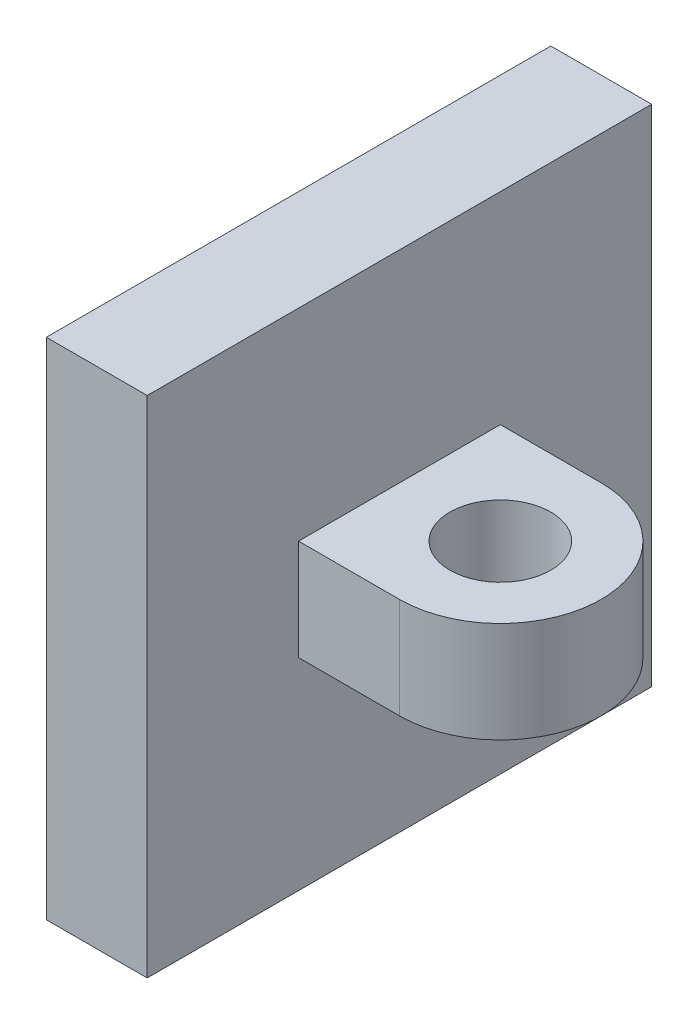
SolidWorks part; units mm, degrees
material "20% infill ABS"
ref_plane "Front Plane" through (0, 0, 0) normal (0, 0, 1) x (1, 0, 0)
ref_plane "Top Plane" through (0, 0, 0) normal (0, 1, 0) x (1, 0, 0)
ref_plane "Right Plane" through (0, 0, 0) normal (1, 0, 0) x (0, 0, -1)
sketch "Sketch1" plane through (0, 0, 0) normal (0, 1, 0) x (1, 0, 0)
  line L1 (-0.7701, 1.6207) -> (1.2299, 1.6207)
  line L2 (-0.7701, 1.6207) -> (-0.7701, -8.3793)
  line L3 (-0.7701, -8.3793) -> (1.2299, -8.3793)
  line L4 (1.2299, 1.6207) -> (1.2299, -8.3793)
  dimension "D1" = 2
  dimension "D2" = 10
extrude "Boss-Extrude1" add sketch "Sketch1" along normal blind 10
sketch "Sketch2" plane through (1.2299, 0, 0) normal (1, 0, 0) x (0, 0, -1)
  line L0 (-8.3793, 10) -> (1.6207, 0)
  line L2 (-5.3793, 4) -> (-1.3793, 4)
  line L3 (-5.3793, 4) -> (-5.3793, 6)
  line L4 (-5.3793, 6) -> (-1.3793, 6)
  line L5 (-1.3793, 4) -> (-1.3793, 6)
  line L6 (-5.3793, 4) -> (-1.3793, 6) construction
  line L7 (-5.3793, 6) -> (-1.3793, 4) construction
  point P4 (-3.3793, 5)
  dimension "D1" = 4
  dimension "D2" = 2
extrude "Boss-Extrude2" add sketch "Sketch2" along normal blind 5 contours L4 L3 L2 L0 | L2 L5 L4 L0
sketch "Sketch3" plane through (0, 6, 0) normal (0, 1, 0) x (1, 0, 0)
  line L0 (6.2299, -3.3793) -> (3.2299, -3.3793)
  line L1 (6.2299, -5.3793) -> (6.2299, -1.3793) construction
  line L2 (6.2299, -1.3793) -> (1.2299, -1.3793) construction
  line L3 (6.2299, -5.3793) -> (1.2299, -5.3793) construction
  line L4 (3.2299, -1.3793) -> (6.2299, -1.3793)
  line L5 (6.2299, -1.3793) -> (6.2299, -5.3793)
  line L6 (6.2299, -5.3793) -> (3.2299, -5.3793)
  circle A0 centre (3.2299, -3.3793) radius 1
  arc A1 (3.2299, -1.3793) -> (3.2299, -5.3793) centre (3.2299, -3.3793) cw
extrude "Cut-Extrude1" cut sketch "Sketch3" against normal blind 15
